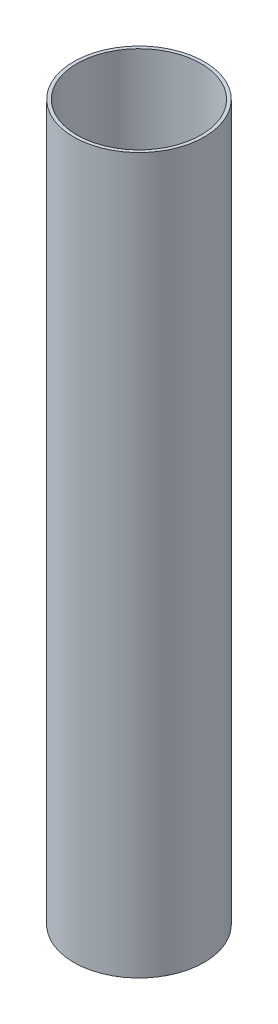
SolidWorks part; units mm, degrees
material "75mm-Phenolic Liner"
ref_plane "Front Plane" through (0, 0, 0) normal (0, 0, 1) x (1, 0, 0)
ref_plane "Top Plane" through (0, 0, 0) normal (0, 1, 0) x (1, 0, 0)
ref_plane "Right Plane" through (0, 0, 0) normal (1, 0, 0) x (0, 0, -1)
sketch "Sketch1" plane through (0, 0, 0) normal (0, 1, 0) x (1, 0, 0)
  circle A0 centre (0, 0) radius 33.147
  circle A1 centre (0, 0) radius 34.8996
  dimension "D1" = 66.294
  dimension "D2" = 69.7992
extrude "Boss-Extrude1" add sketch "Sketch1" along normal blind 382.1938
